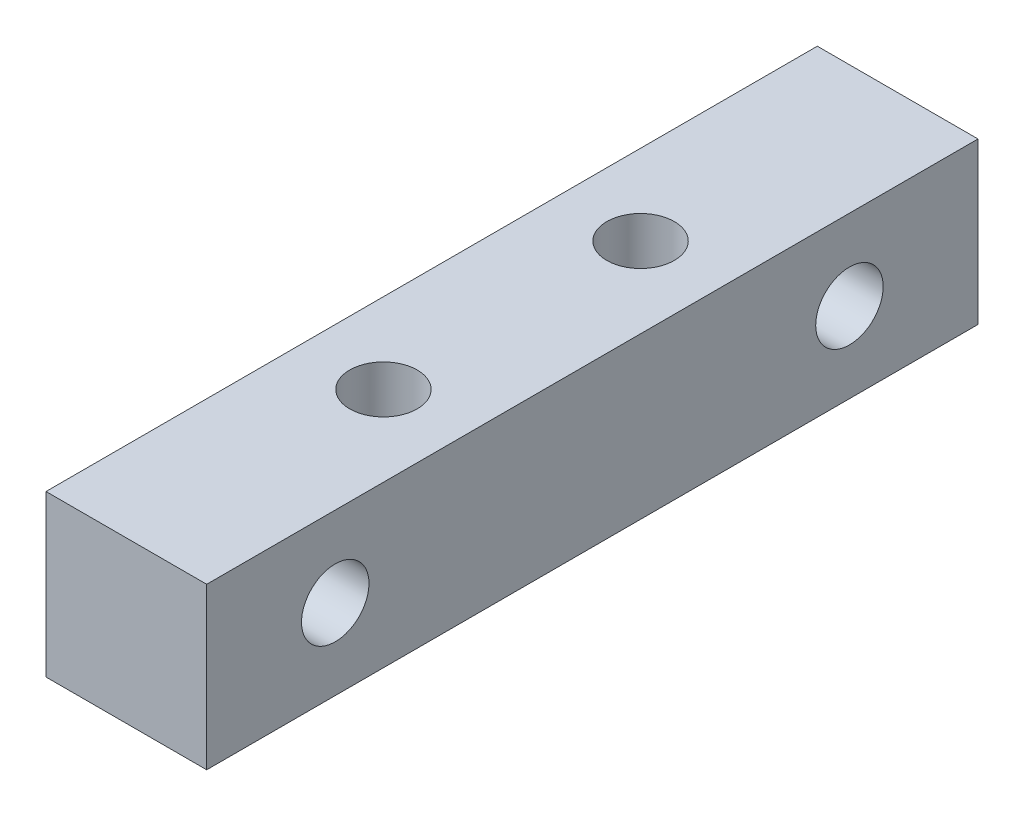
SolidWorks part; units mm, degrees
ref_plane "前视基准面" through (0, 0, 0) normal (0, 0, 1) x (1, 0, 0)
ref_plane "上视基准面" through (0, 0, 0) normal (0, 1, 0) x (1, 0, 0)
ref_plane "右视基准面" through (0, 0, 0) normal (1, 0, 0) x (0, 0, -1)
sketch "草图1" plane through (0, 0, 0) normal (0, 0, 1) x (1, 0, 0)
  line L1 (0, 0) -> (10, 0)
  line L2 (0, 0) -> (0, -10)
  line L3 (0, -10) -> (10, -10)
  line L4 (10, 0) -> (10, -10)
extrude "凸台-拉伸1" add sketch "草图1" along normal blind 48
sketch "草图2" plane through (10, 0, 0) normal (1, 0, 0) x (0, 0, -1)
  circle A0 centre (-40, -5) radius 2.1
  circle A1 centre (-8, -5) radius 2.1
extrude "切除-拉伸1" cut sketch "草图2" against normal blind 48
sketch "草图3" plane through (0, 0, 0) normal (0, 1, 0) x (1, 0, 0)
  circle A0 centre (5, -16) radius 2.1
  circle A1 centre (5, -32) radius 2.1
extrude "切除-拉伸2" cut sketch "草图3" against normal blind 48
